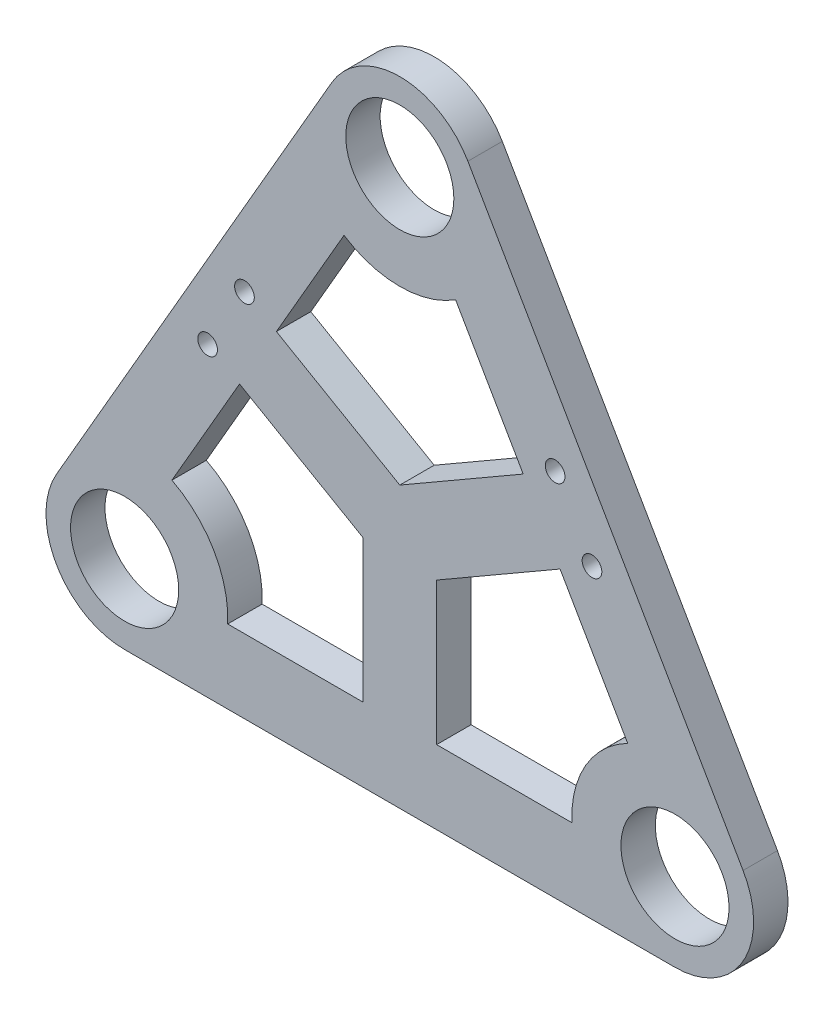
SolidWorks part; units mm, degrees
ref_plane "Front Plane" through (0, 0, 0) normal (0, 0, 1) x (1, 0, 0)
ref_plane "Top Plane" through (0, 0, 0) normal (0, 1, 0) x (1, 0, 0)
ref_plane "Right Plane" through (0, 0, 0) normal (1, 0, 0) x (0, 0, -1)
sketch "Sketch1" plane through (0, 0, 0) normal (0, 0, 1) x (1, 0, 0)
  line L0 (3.85, 0) -> (-3.85, 0) construction
  line L1 (42.1436, 104.9948) -> (-13.8564, 8)
  line L2 (69.8564, 104.9948) -> (125.8564, 8)
  line L3 (0, -16) -> (112, -16)
  circle A0 centre (0, 0) radius 11
  circle A1 centre (112, 0) radius 11
  arc A2 (-13.8564, 8) -> (0, -16) centre (0, 0) ccw
  arc A3 (112, -16) -> (125.8564, 8) centre (112, 0) ccw
  circle A4 centre (56, 96.9948) radius 11
  arc A5 (69.8564, 104.9948) -> (42.1436, 104.9948) centre (56, 96.9948) ccw
  dimension "D1" = 22
  dimension "D2" = 22
  dimension "D3" = 32
  dimension "D4" = 32
  dimension "D5" = 112
  dimension "D6" = 22
  dimension "D7" = 32
  dimension "D8" = 112
  dimension "D9" = 112
extrude "Boss-Extrude1" add sketch "Sketch1" along normal blind 7
sketch "Sketch2" plane through (0, 0, 7) normal (0, 0, 1) x (1, 0, 0)
  line L0 (9.6221, 18.6659) -> (23.384, 42.5022)
  line L1 (23.384, 42.5022) -> (48.5, 28.0015)
  line L2 (48.5, 28.0015) -> (48.5, -1)
  line L3 (48.5, -1) -> (20.9762, -1)
  line L4 (42.1436, 104.9948) -> (-13.8564, 8) construction
  line L5 (63.5, -1) -> (91.0238, -1)
  line L6 (63.5, -1) -> (63.5, 28.0015)
  line L7 (63.5, 28.0015) -> (88.616, 42.5022)
  line L8 (88.616, 42.5022) -> (102.3779, 18.6659)
  line L9 (125.8564, 8) -> (69.8564, 104.9948) construction
  line L10 (30.884, 55.4926) -> (44.6459, 79.3289)
  line L11 (30.884, 55.4926) -> (56, 40.9919)
  line L12 (56, 40.9919) -> (81.116, 55.4926)
  line L13 (81.116, 55.4926) -> (67.3541, 79.3289)
  line L14 (0, -16) -> (112, -16) construction
  line L15 (56, -16) -> (56, 32.3316) construction
  line L16 (97.8564, 56.4974) -> (56, 32.3316) construction
  line L17 (56, 32.3316) -> (14.1436, 56.4974) construction
  arc A0 (20.9762, -1) -> (9.6221, 18.6659) centre (0, 0) ccw
  circle A1 centre (0, 0) radius 11 construction
  arc A2 (44.6459, 79.3289) -> (67.3541, 79.3289) centre (56, 96.9948) ccw
  circle A3 centre (56, 96.9948) radius 11 construction
  arc A4 (102.3779, 18.6659) -> (91.0238, -1) centre (112, 0) ccw
  circle A5 centre (112, 0) radius 11 construction
  point P31 (35.942, 35.2519)
  dimension "D1" = 10
  dimension "D2" = 10
  dimension "D3" = 10
  dimension "D4" = 15
  dimension "D5" = 15
  dimension "D6" = 15
  dimension "D7" = 15
  dimension "D8" = 15
  dimension "D9" = 15
  dimension "D10" = 7.5
  dimension "D11" = 7.5
  dimension "D12" = 7.5
extrude "Cut-Extrude1" cut sketch "Sketch2" against normal through all
sketch "Sketch5" plane through (0, 0, 7) normal (0, 0, 1) x (1, 0, 0)
  line L0 (24.3888, 59.2426) -> (16.8888, 46.2522) construction
  line L1 (42.1436, 104.9948) -> (-13.8564, 8) construction
  line L2 (20.6388, 52.7474) -> (14.1436, 56.4974) construction
  line L3 (87.6112, 59.2426) -> (95.1112, 46.2522) construction
  line L4 (125.8564, 8) -> (69.8564, 104.9948) construction
  circle A0 centre (24.3888, 59.2426) radius 2
  circle A1 centre (16.8888, 46.2522) radius 2
  circle A2 centre (87.6112, 59.2426) radius 2
  circle A3 centre (95.1112, 46.2522) radius 2
  dimension "D1" = 4
  dimension "D2" = 4
  dimension "D5" = 4
  dimension "D6" = 4
  dimension "D3" = 7.5
  dimension "D4" = 15
  dimension "D7" = 7.5
extrude "Cut-Extrude2" cut sketch "Sketch5" against normal through all
